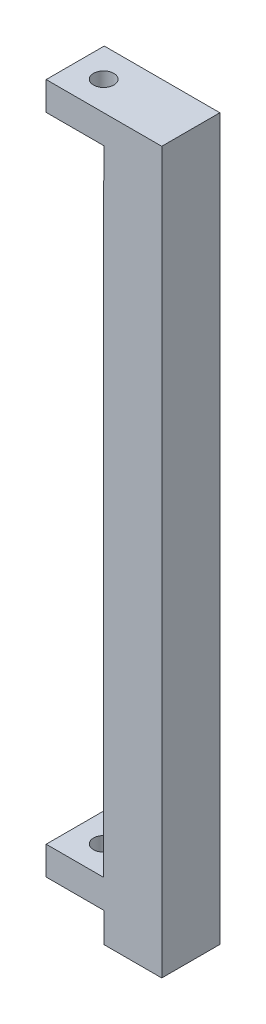
SolidWorks part; units mm, degrees
ref_plane "Front Plane" through (0, 0, 0) normal (0, 0, 1) x (1, 0, 0)
ref_plane "Top Plane" through (0, 0, 0) normal (0, 1, 0) x (1, 0, 0)
ref_plane "Right Plane" through (0, 0, 0) normal (1, 0, 0) x (0, 0, -1)
sketch "Sketch1" plane through (0, 0, 0) normal (0, 0, 1) x (1, 0, 0)
  line L0 (0, 0) -> (0, 5)
  line L1 (0, 5) -> (-10, 5)
  line L2 (-10, 5) -> (-10, 10)
  line L3 (-10, 10) -> (0, 10)
  line L4 (0, 10) -> (0, 119)
  line L5 (0, 119) -> (-10, 119)
  line L6 (-10, 119) -> (-10, 124)
  line L7 (-10, 124) -> (10, 124)
  line L10 (10, 124) -> (10, 0)
  line L11 (10, 0) -> (0, 0)
  dimension "D1" = 10
  dimension "D2" = 5
  dimension "D3" = 5
  dimension "D4" = 5
  dimension "D6" = 10
  dimension "D7" = 10
  dimension "D8" = 109
extrude "Boss-Extrude1" add sketch "Sketch1" against normal blind 10
sketch "Sketch2" plane through (0, 0, 0) normal (0, 0, 1) x (1, 0, 0)
  line L0 (-10, 10) -> (-10, 5)
  line L1 (-10, 5) -> (0, 5)
  line L2 (0, 5) -> (0, 0)
  line L3 (-10, 124) -> (-10, 119)
  line L4 (-10, 119) -> (0, 119)
  line L5 (0, 119) -> (0, 113.9)
  line L6 (0, 119) -> (0, 10) construction
  line L7 (-9.9, 124) -> (-9.9, 119.1)
  line L8 (-9.9, 119.1) -> (0.1, 119.1)
  line L9 (0.1, 119.1) -> (0.1, 113.9)
  line L10 (-9.9, 10) -> (-9.9, 5.1)
  line L11 (-9.9, 5.1) -> (0.1, 5.1)
  line L12 (0.1, 5.1) -> (0.1, 0)
  line L13 (-10, 10) -> (-9.9, 10)
  line L14 (0, 0) -> (0.1, 0)
  line L15 (0, 113.9) -> (0.1, 113.9)
  line L16 (-10, 124) -> (-9.9, 124)
  dimension "D1" = 5.1
  dimension "D2" = 0.1
extrude "Cut-Extrude1" cut sketch "Sketch2" against normal through all
sketch "Sketch3" plane through (0, 5.1, 0) normal (0, -1, 0) x (1, 0, 0)
  line L0 (0.1, -10) -> (-9.9, -10) construction
  line L1 (-10, 0) -> (0, 0) construction
  line L2 (-10, 0) -> (-10, -10) construction
  line L3 (-10, -10) -> (0, -10) construction
  line L4 (0, 0) -> (0, -10) construction
  line L5 (-9.9, -10) -> (-9.9, 0) construction
  line L6 (0.1, -10) -> (0.1, 0) construction
  line L7 (0.1, 0) -> (-9.9, 0) construction
  line L8 (-10, 0) -> (0, -10) construction
  circle A0 centre (-5, -5) radius 1.75
  dimension "D3" = 3.5
  dimension "D1" = 0.1
  dimension "D2" = 0.1
extrude "Cut-Extrude2" cut sketch "Sketch3" against normal through all
